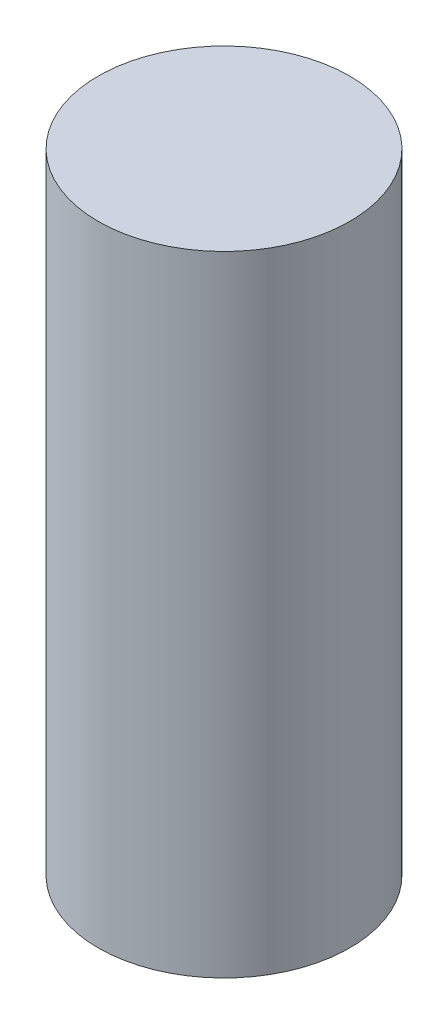
SolidWorks part; units mm, degrees
ref_plane "前视基准面" through (0, 0, 0) normal (0, 0, 1) x (1, 0, 0)
ref_plane "上视基准面" through (0, 0, 0) normal (0, 1, 0) x (1, 0, 0)
ref_plane "右视基准面" through (0, 0, 0) normal (1, 0, 0) x (0, 0, -1)
sketch "草图1" plane through (0, 0, 0) normal (0, 1, 0) x (1, 0, 0)
  circle A0 centre (0, 0) radius 5
  dimension "D1" = 10
extrude "凸台-拉伸1" add sketch "草图1" along normal blind 25
